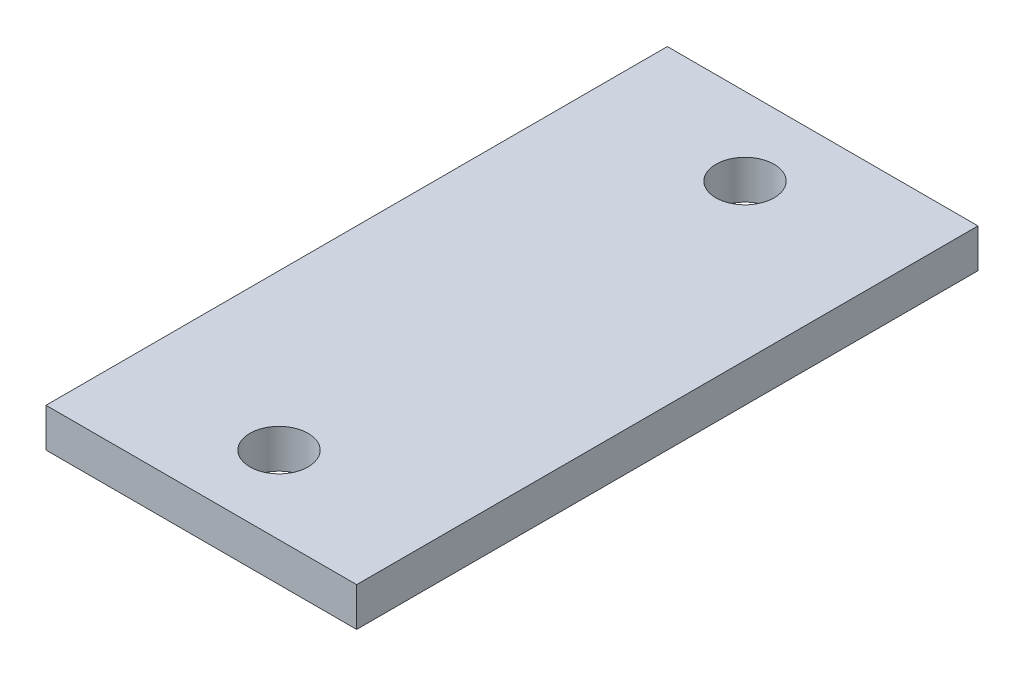
SolidWorks part; units mm, degrees
material "Plain Carbon Steel"
ref_plane "Front Plane" through (0, 0, 0) normal (0, 0, 1) x (1, 0, 0)
ref_plane "Top Plane" through (0, 0, 0) normal (0, 1, 0) x (1, 0, 0)
ref_plane "Right Plane" through (0, 0, 0) normal (1, 0, 0) x (0, 0, -1)
sketch "Sketch1" plane through (0, 0, 0) normal (0, 1, 0) x (1, 0, 0)
  line L1 (0, 0) -> (50.8, 0)
  line L2 (0, 0) -> (0, 101.6)
  line L3 (0, 101.6) -> (50.8, 101.6)
  line L4 (50.8, 0) -> (50.8, 101.6)
  line L8 (0, 12.7) -> (50.8, 12.7) construction
  circle A0 centre (25.4, 12.7) radius 4.7625
  circle A1 centre (25.4, 88.9) radius 4.7625
  dimension "D6" = 9.525
  dimension "D1" = 101.6
  dimension "D2" = 88.9
  dimension "D3" = 25.4
  dimension "D5" = 50.8
  dimension "D7" = 88.9
extrude "Hammer" add sketch "Sketch1" along normal blind 6.35
